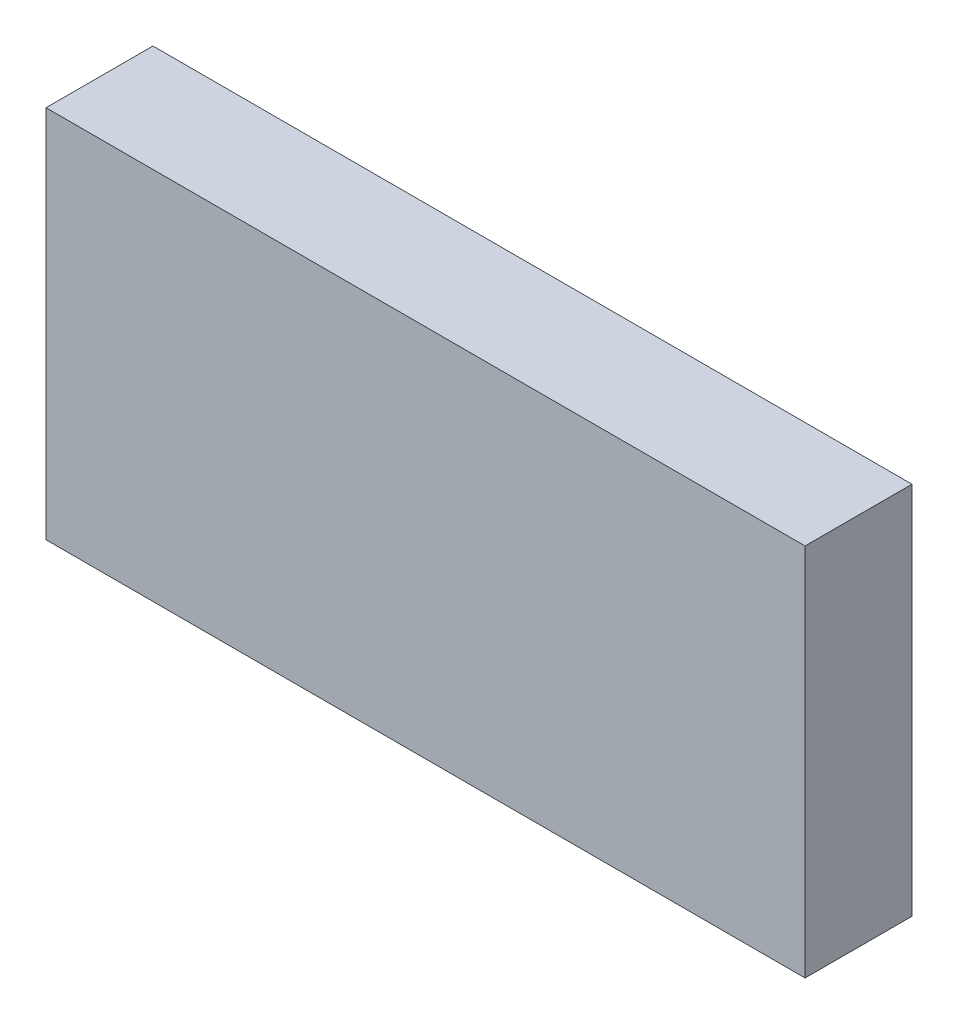
SolidWorks part; units mm, degrees
ref_plane "Front Plane" through (0, 0, 0) normal (0, 0, 1) x (1, 0, 0)
ref_plane "Top Plane" through (0, 0, 0) normal (0, 1, 0) x (1, 0, 0)
ref_plane "Right Plane" through (0, 0, 0) normal (1, 0, 0) x (0, 0, -1)
sketch "Sketch1" plane through (0, 0, 0) normal (0, 0, 1) x (1, 0, 0)
  line L0 (-3.55, 1.75) -> (3.55, 1.75)
  line L1 (3.55, 1.75) -> (3.55, -1.75)
  line L2 (3.55, -1.75) -> (-3.55, -1.75)
  line L3 (-3.55, -1.75) -> (-3.55, 1.75)
extrude "Component_Outline" add sketch "Sketch1" along normal blind 1 separate body
sketch3d "3DSketch1"
  line L0 (0, 0, 0) -> (1, 0, 0)
  line L1 (0, 0, 0) -> (0, 1, 0)
  line L2 (0, 0, 0) -> (0, 0, 1)
  point P0 (0, 0, 0)
